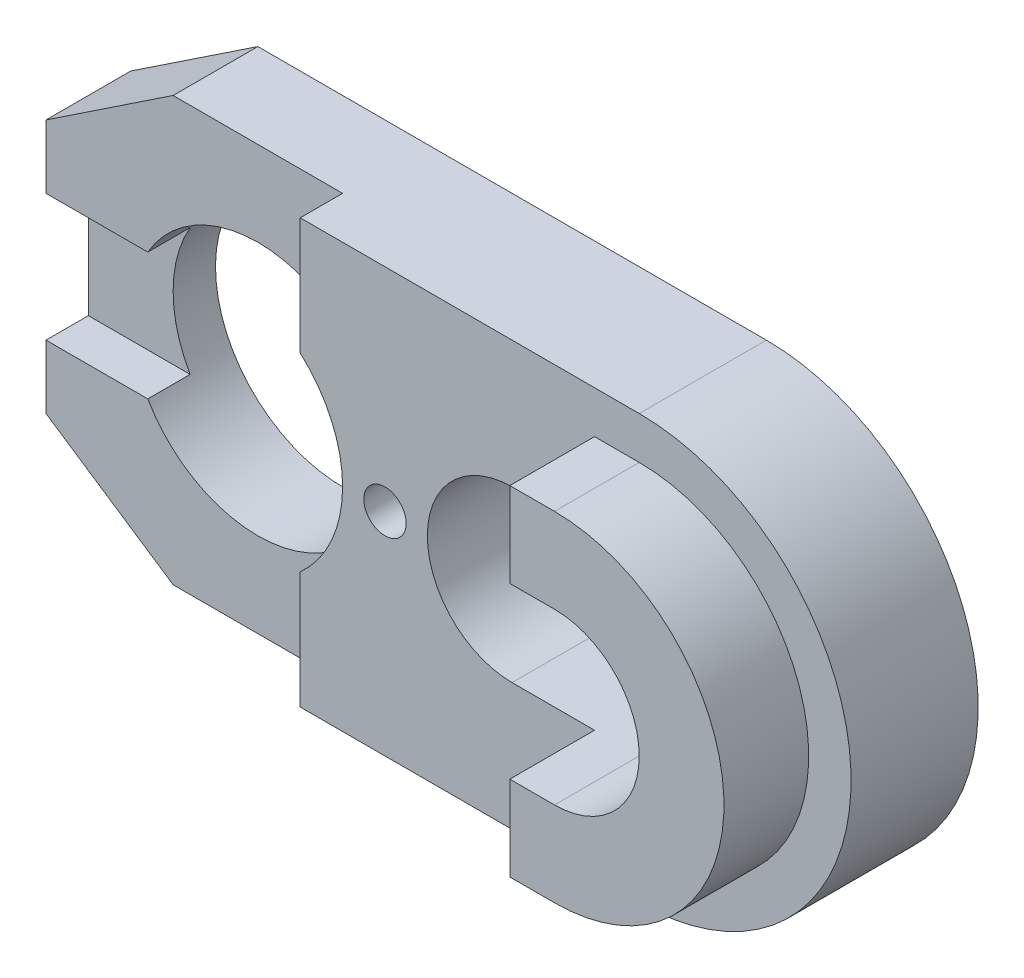
SolidWorks part; units mm, degrees
ref_plane "Front" through (0, 0, 0) normal (0, 0, 1) x (1, 0, 0)
ref_plane "Top" through (0, 0, 0) normal (0, 1, 0) x (1, 0, 0)
ref_plane "Right" through (0, 0, 0) normal (1, 0, 0) x (0, 0, -1)
sketch "Sketch1" plane through (0, 0, 0) normal (0, 0, 1) x (1, 0, 0)
  line L0 (-9.4958, 3) -> (-6.4958, 5)
  line L1 (-6.4958, -5) -> (5.5042, -5)
  line L2 (-9.4958, -3) -> (-9.4958, 3)
  line L3 (-6.4958, 5) -> (5.5042, 5)
  line L5 (-9.4958, -3) -> (-6.4958, -5)
  line L6 (2.5042, 0) -> (5.5042, 0) construction
  line L7 (2.5042, 2) -> (5.5042, 2)
  line L8 (2.5042, -2) -> (5.5042, -2)
  arc A0 (5.5042, -5) -> (10.5042, -0.02) centre (5.5042, 0) ccw
  arc A1 (5.5042, 5) -> (10.5042, -0.02) centre (5.5042, 0) cw
  circle A2 centre (-4.4958, 0) radius 3
  circle A3 centre (-0.4958, 0) radius 0.5
  arc A4 (2.5042, 2) -> (2.5042, -2) centre (2.5042, 0) ccw
  arc A5 (5.5042, -2) -> (5.5042, 2) centre (5.5042, 0) ccw
  point P0 (0, 0)
  point P16 (4.0042, 0)
  dimension "D3" = 5
  dimension "D1" = 6
  dimension "D8" = 1
  dimension "D11" = 2
  dimension "D2" = 3
  dimension "D4" = 5
  dimension "D5" = 3
  dimension "D6" = 2
  dimension "D7" = 2
  dimension "D9" = 4
  dimension "D10" = 3
  dimension "D12" = 3
  dimension "D13" = 12
extrude "Boss-Extrude1" add sketch "Sketch1" along normal blind 5
sketch "Sketch2" plane through (0, 5, 0) normal (0, 1, 0) x (1, 0, 0)
  line L0 (-9.4958, -2) -> (-2.4958, -2)
  line L1 (-9.4958, -5) -> (-9.4958, 0) construction
  line L2 (-2.4958, -2) -> (-2.4958, -3)
  line L3 (-2.4958, -3) -> (4.4501, -3)
  line L4 (4.4501, -3) -> (4.4501, -5)
  line L5 (5.5042, -5) -> (-6.4958, -5) construction
  line L6 (4.4501, -5) -> (9.5042, -5)
  line L7 (5.5042, -5) -> (10.5042, -5) construction
  line L8 (9.5042, -5) -> (9.5042, -3)
  line L9 (9.5042, -3) -> (10.5042, -3)
  line L10 (10.5042, -5) -> (10.5042, 0) construction
  line L11 (10.5042, -3) -> (10.5042, -6.6431)
  line L12 (10.5042, -6.6431) -> (-9.4958, -6.6431)
  line L13 (-9.4958, -6.6431) -> (-9.4958, -2)
  point P18 (-5.9958, -2)
  dimension "D1" = 7
  dimension "D2" = 1
  dimension "D3" = 3
  dimension "D4" = 2
  dimension "D5" = 1
extrude "Cut-Extrude1" cut sketch "Sketch2" against normal blind 25
sketch "Sketch3" plane through (0, 0, 5) normal (0, 0, 1) x (1, 0, 0)
  line L0 (5.5042, 0) -> (2.5042, 0) construction
  line L1 (5.5042, -2) -> (2.5042, -2)
  line L2 (5.5042, 2) -> (2.5042, 2)
  line L3 (5.5042, 0) -> (2.5042, 0) construction
  line L4 (5.5042, -4) -> (2.5042, -4)
  line L5 (5.5042, 4) -> (2.5042, 4)
  line L6 (4.4293, 4) -> (4.4293, 6.2199)
  line L7 (4.4293, 6.2199) -> (11.8433, 6.2199)
  line L8 (11.8433, 6.2199) -> (11.8433, -6.3652)
  line L9 (11.8433, -6.3652) -> (4.4293, -6.5729)
  line L10 (4.4293, -6.5729) -> (4.4501, -5)
  arc A0 (5.5042, -2) -> (5.5042, 2) centre (5.5042, 0) ccw
  arc A1 (2.5042, 2) -> (2.5042, -2) centre (2.5042, 0) ccw
  arc A2 (5.5042, -4) -> (5.5042, 4) centre (5.5042, 0) ccw
  arc A3 (2.5042, 4) -> (2.5042, -4) centre (2.5042, 0) ccw
  point P4 (4.0042, 0)
  point P11 (4.0042, 0)
  line M1 (5.5042, 5) -> (4.4501, 5)
  line M2 (4.4501, 5) -> (4.4501, 2)
  line M6 (4.4501, -2) -> (4.4501, -5)
  line M7 (4.4501, -5) -> (5.5042, -5)
  arc M8 (5.5042, -5) -> (9.5042, -3) centre (5.5042, 0) ccw
  line M9 (9.5042, -3) -> (9.5042, 3)
  arc M10 (9.5042, 3) -> (5.5042, 5) centre (5.5042, 0) ccw
  dimension "D1" = 2
  dimension "D2" = 4
extrude "Cut-Extrude2" cut sketch "Sketch3" against normal blind 2 contours A2 L5 M9 M10 M1 M2 | A2 L4 M6 M7 M8 M9 | L5 A3 L4 L1 A1 L2 M6 M2
sketch "Sketch4" plane through (-9.4958, 0, 0) normal (-1, 0, 0) x (0, 0, 1)
  line L0 (2, -3) -> (2, 3) construction
  line L1 (2, 1.5) -> (1, 1.5)
  line L2 (2, 1.5) -> (2, -1.5)
  line L3 (2, -1.5) -> (1, -1.5)
  line L4 (1, 1.5) -> (1, -1.5)
  dimension "D1" = 1
  dimension "D2" = 3
  dimension "D3" = 1.5
extrude "Cut-Extrude3" cut sketch "Sketch4" against normal blind 3
